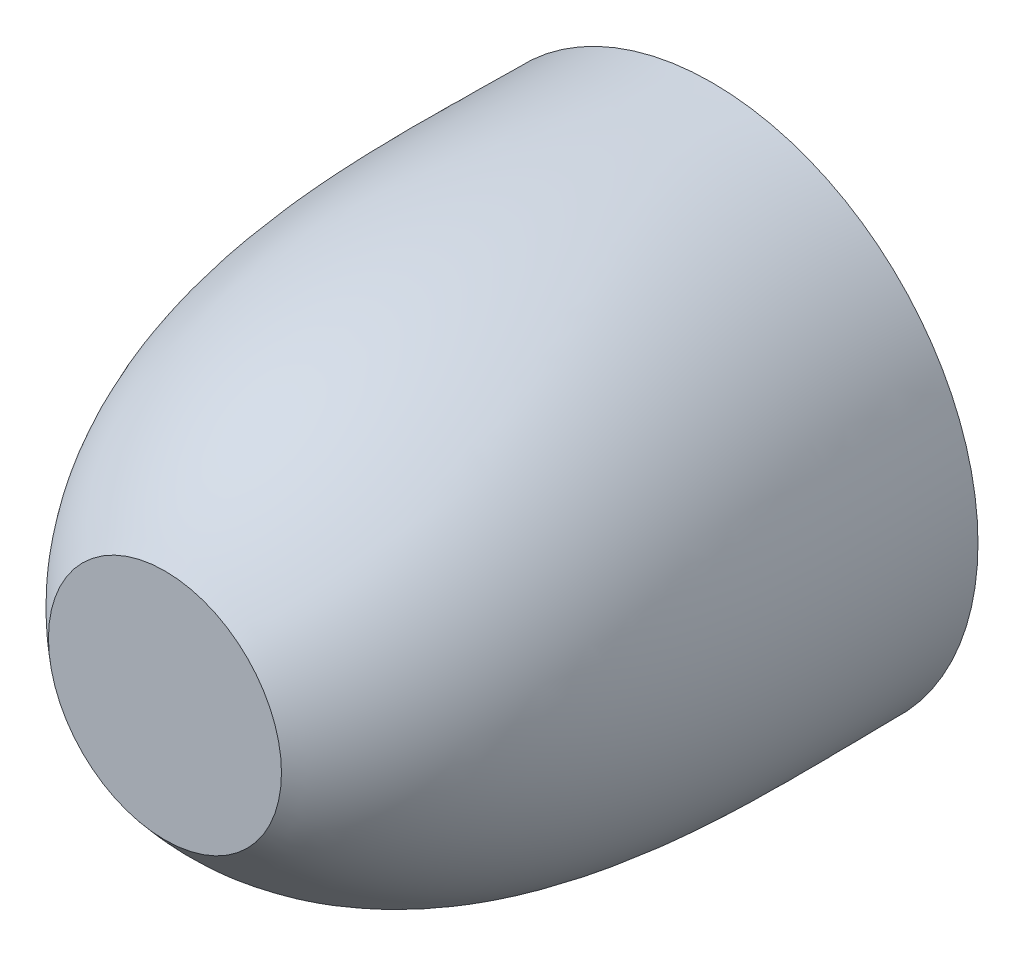
SolidWorks part; units mm, degrees
ref_plane "Front" through (0, 0, 0) normal (0, 0, 1) x (1, 0, 0)
ref_plane "Top" through (0, 0, 0) normal (0, 1, 0) x (1, 0, 0)
ref_plane "Right" through (0, 0, 0) normal (1, 0, 0) x (0, 0, -1)
sketch "Sketch1" plane through (0, 0, 0) normal (0, 1, 0) x (1, 0, 0)
  line L0 (0, 0) -> (0, 11617.8097) construction
  line L1 (22.25, 43.1402) -> (22.25, 50043.1402) construction
  line L2 (10, 0) -> (0, 0)
  line L3 (11.5, -4) -> (0, -4)
  line L4 (22.25, 50) -> (26.25, 50)
  line L5 (10, 0) -> (0, 0) construction
  line L6 (11.5, -4) -> (0, -4) construction
  line L7 (0, -4) -> (0, 0)
  spline S0 degree 3 poles (10, 0) (24.0344, 12.2482) (22.25, 34.2571) (22.25, 50) knots 0 0 0 0 1 1 1 1
  spline S1 degree 1 poles (11.5, -4) (26.25, 50) knots 0 0 1 1 construction
  spline S2 degree 3 poles (11.5, -4) (11.7252, -3.8035) (12.0674, -3.5047) (12.5058, -3.1223) (13.004, -2.687) (13.631, -2.1106) (14.5866, -1.1779) (15.7185, 0.0323) (17.388, 2.0444) (19.2213, 4.6922) (21.649, 9.1496) (23.8235, 15.0335) (25.3611, 22.3395) (26.1162, 29.6935) (26.3117, 35.7067) (26.3295, 40.3504) (26.3027, 43.7249) (26.2708, 46.4198) (26.2536, 48.5007) (26.25, 49.4965) (26.25, 50) knots -0.026842 -0.026842 -0.026842 -0.026842 -0.010798 -0.002775 0.005247 0.021291 0.037336 0.069424 0.101513 0.165691 0.229868 0.358224 0.486579 0.614934 0.743289 0.807467 0.871645 0.935822 0.967911 1 1 1 1
  point P5 (0, 0)
  point P14 (15.5941, 6.2982)
  point P15 (0, -4)
  point P17 (0, 0)
  point P18 (19.7764, 16.0936)
  point P19 (0, 0)
  dimension "D1" = 22.25
  dimension "D2" = 50
  dimension "D4" = 10
  dimension "D5" = 11.5
  dimension "D6" = 16
  dimension "D7" = 9.7483
  dimension "D3" = 4
revolve "shell" add sketch "Sketch1" angle 360 about L0
sketch "Sketch2" plane through (0, 0, -50) normal (0, 0, -1) x (-1, 0, 0)
  line L0 (0, 0) -> (0, 22.25) construction
  line L1 (2, 4.5826) -> (2, 22.1599)
  line L2 (-2, 4.5826) -> (-2, 22.1599)
  line L3 (3.7403, 3.3182) -> (20.4573, 8.7499)
  line L4 (4.9763, -0.486) -> (21.6934, 4.9457)
  line L5 (4.3116, -2.5318) -> (14.6433, -16.7522)
  line L6 (1.0755, -4.883) -> (11.4072, -19.1033)
  line L7 (-1.0755, -4.883) -> (-11.4072, -19.1033)
  line L8 (-4.3116, -2.5318) -> (-14.6433, -16.7522)
  line L9 (-4.9763, -0.486) -> (-21.6934, 4.9457)
  line L10 (-3.7403, 3.3182) -> (-20.4573, 8.7499)
  line L11 (0, 0) -> (2, 4.5826) construction
  circle A0 centre (0, 0) radius 22.25 construction
  circle A1 centre (0, 0) radius 22.25
  circle A2 centre (0, 0) radius 5
  circle A3 centre (0, 0) radius 1.5
  point P10 (0, 0)
  point P11 (0, 0)
  point P30 (0, 0)
  point P31 (4.9688, -0.5577)
  circle M9 centre (0, 0) radius 22.25
  dimension "D1" = 10
  dimension "D2" = 3
  dimension "D3" = 4
  dimension "D5" = 5
  dimension "D4" = 5
extrude "Boss-Extrude1" add sketch "Sketch2" against normal blind 2 from offset 5 separate body contours A2 L6 L5 M9 | A2 A3 | A2 L8 L7 M9 | A2 L10 L9 M9 | A2 L1 L2 M9 | A2 L4 L3 M9
